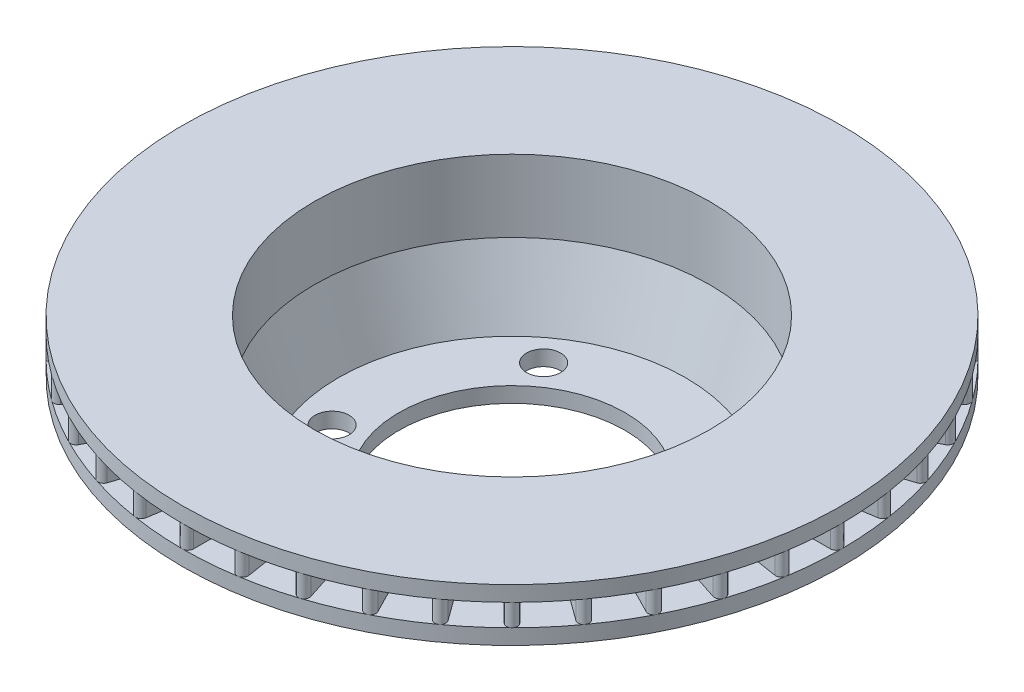
SolidWorks part; units mm, degrees
ref_plane "Front Plane" through (0, 0, 0) normal (0, 0, 1) x (1, 0, 0)
ref_plane "Top Plane" through (0, 0, 0) normal (0, 1, 0) x (1, 0, 0)
ref_plane "Right Plane" through (0, 0, 0) normal (1, 0, 0) x (0, 0, -1)
sketch "Sketch1" plane through (0, 0, 0) normal (0, 1, 0) x (1, 0, 0)
  circle A0 centre (0, 0) radius 97
  dimension "D1" = 194
extrude "Boss-Extrude1" add sketch "Sketch1" along normal blind 10 and the other way blind 37 draft 19.359
shell "Shell1" thickness 7
sketch "Sketch2" plane through (0, 10, 0) normal (0, 1, 0) x (1, 0, 0)
  circle A0 centre (0, 0) radius 90 construction
  circle A1 centre (0, 0) radius 90
  circle A2 centre (0, 0) radius 150
  point P4 (0, 0)
  dimension "D1" = 300
extrude "Boss-Extrude2" add sketch "Sketch2" along normal blind 7
sketch "Sketch3" plane through (0, 17, 0) normal (0, 1, 0) x (1, 0, 0)
  circle A0 centre (0, 0) radius 90 construction
  circle A1 centre (0, 0) radius 90
extrude "Extrude-Thin1" add sketch "Sketch3" along normal blind 10 thin
sketch "Sketch4" plane through (0, 27, 0) normal (0, 1, 0) x (1, 0, 0)
  circle A0 centre (0, 0) radius 90 construction
  circle A1 centre (0, 0) radius 90
  circle A2 centre (0, 0) radius 150 construction
  circle A3 centre (0, 0) radius 150
extrude "Boss-Extrude3" add sketch "Sketch4" along normal blind 7
sketch "Sketch5" plane through (0, 0, 0) normal (0, 0, 1) x (1, 0, 0)
  line L0 (97, 27) -> (97, 17)
  line L1 (-97, 27) -> (97, 27) construction
  line L2 (-150, 27) -> (150, 27) construction
  line L3 (150, 17) -> (-150, 17) construction
  line L4 (97, 17) -> (-97, 17) construction
  line L5 (97, 17) -> (107, 17)
  line L6 (107, 17) -> (97, 27)
  line L7 (0, 62.4957) -> (0, -65.2484) construction
revolve "Revolve1" add sketch "Sketch5" angle 360 about L7
sketch "Sketch6" plane through (0, 17, 0) normal (0, 1, 0) x (1, 0, 0)
  line L0 (0, 186.5889) -> (0, -191.9627) construction
  line L1 (0, 147.5) -> (0, 92.5) construction
  line L2 (2.5, 147.5) -> (2.5, 92.5)
  line L3 (-2.5, 147.5) -> (-2.5, 92.5)
  arc A0 (2.5, 147.5) -> (-2.5, 147.5) centre (0, 147.5) ccw
  arc A1 (-2.5, 92.5) -> (2.5, 92.5) centre (0, 92.5) ccw
  circle A2 centre (0, 0) radius 150 construction
  circle A3 centre (0, 0) radius 90 construction
  point P5 (0, 120)
  dimension "D1" = 5
extrude "Boss-Extrude4" add sketch "Sketch6" along normal up to surface (10 mm away) up to face at (0, 27, 150)
pattern_circular "CirPattern1" count 40 over 360 about axis through (0, 0, 0) along (0, 1, 0) of "Boss-Extrude4"
sketch "Sketch7" plane through (0, -37, 0) normal (0, -1, 0) x (1, 0, 0)
  circle A0 centre (0, 0) radius 65 construction
  dimension "D1" = 130
hole_wizard "Ø15.5 (15.5) Diameter Hole1" positions "Sketch8" profile "Sketch10" hole size "Ø15.5" standard "ISO" end condition through all
sketch "Sketch8" plane through (0, -37, 0) normal (0, -1, 0) x (-1, 0, 0)
  circle A0 centre (0, 0) radius 65 construction
  point P0 (0, -65)
  point P5 (0, 0)
sketch "Sketch10" plane through (0, -37, 65) normal (1, 0, 0) x (0, 0, -1)
  line L0 (0, 0) -> (0, 71)
  line L1 (0, 71) -> (7.75, 71)
  line L2 (7.75, 71) -> (7.75, 0)
  line L5 (7.75, 0) -> (0, 0)
  line L11 (0, -6.35) -> (0, 107.95) construction
  dimension "Thru Hole Dia." = 15.5
  dimension "Thru Hole Depth" = 71
pattern_circular "CirPattern2" count 5 over 360 about axis through (0, 0, 0) along (0, 1, 0) of "Ø15.5 (15.5) Diameter Hole1"
fillet "Fillet1" radius 2 1 edges at (0, -37, 84.0001)
sketch "Sketch11" plane through (0, -37, 0) normal (0, -1, 0) x (1, 0, 0)
  circle A0 centre (0, 0) radius 51.5
  dimension "D1" = 103
extrude "Cut-Extrude1" cut sketch "Sketch11" against normal blind 7
